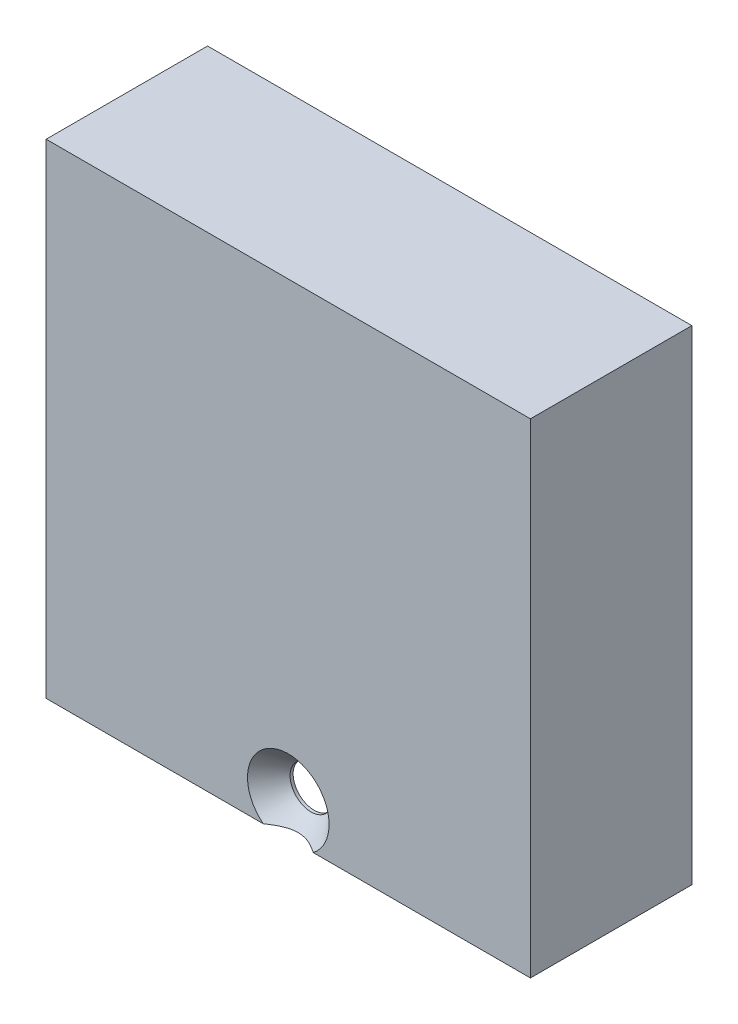
SolidWorks part; units mm, degrees
ref_plane "Plan de face" through (0, 0, 0) normal (0, 0, 1) x (1, 0, 0)
ref_plane "Plan de dessus" through (0, 0, 0) normal (0, 1, 0) x (1, 0, 0)
ref_plane "Plan de droite" through (0, 0, 0) normal (1, 0, 0) x (0, 0, -1)
sketch "Esquisse1" plane through (0, 0, 0) normal (0, 0, 1) x (1, 0, 0)
  line L1 (0, 0) -> (30, 0)
  line L2 (0, 0) -> (0, 30)
  line L3 (0, 30) -> (30, 30)
  line L4 (30, 0) -> (30, 30)
  dimension "D1" = 30
  dimension "D2" = 30
extrude "Main" add sketch "Esquisse1" along normal blind 10
sketch "Esquisse2" plane through (0, 0, 0) normal (0, -1, 0) x (1, 0, 0)
  line L0 (2.75, 0) -> (2.75, 5.2)
  line L1 (0, 0) -> (30, 0) construction
  line L2 (2.75, 5.2) -> (3.35, 5.2)
  line L3 (3.35, 5.2) -> (3.35, 6.2)
  line L4 (3.35, 6.2) -> (2.75, 6.2)
  line L5 (2.75, 6.2) -> (2.75, 8.4)
  line L6 (2.75, 8.4) -> (27.25, 8.4)
  line L7 (27.25, 8.4) -> (27.25, 6.2)
  line L8 (27.25, 6.2) -> (26.65, 6.2)
  line L9 (26.65, 6.2) -> (26.65, 5.2)
  line L10 (26.65, 5.2) -> (27.25, 5.2)
  line L11 (27.25, 5.2) -> (27.25, 0)
  line L12 (27.25, 0) -> (2.75, 0)
  line L13 (0, 10) -> (30, 10) construction
  point P13 (15, 0)
  dimension "D1" = 24.5
  dimension "D2" = 0.6
  dimension "D3" = 1
  dimension "D4" = 2.2
  dimension "D5" = 8.4
  dimension "D6" = 5.2
extrude "Main Fix" cut sketch "Esquisse2" against normal blind 28.5
sketch "Esquisse4" plane through (0, 0, 8.4) normal (0, 0, -1) x (-1, 0, 0)
  line L3 (-27.25, 28.5) -> (-27.25, 0) construction
  line L4 (-2.75, 28.5) -> (-2.75, 0) construction
  line L5 (-27.25, 15.5) -> (-27.25, 28.5)
  line L6 (-27.25, 28.5) -> (-2.75, 28.5)
  line L7 (-2.75, 28.5) -> (-2.75, 15.5)
  line L8 (-2.75, 28.5) -> (-27.25, 28.5) construction
  arc A0 (-27.25, 15.5) -> (-2.75, 15.5) centre (-15, 15.5) cw
  dimension "D1" = 12.25
  dimension "D2" = 13
extrude "Boss.-Extru.2" add sketch "Esquisse4" along normal up to surface (8.4 mm away) up to face at (15, 14.625, 0)
sketch "Esquisse5" plane through (0, 0, 5.2) normal (0, 0, -1) x (-1, 0, 0)
  line L0 (-3.35, 13.9703) -> (0, 13.9703)
  line L1 (0, 13.9703) -> (0, 30)
  line L2 (0, 30) -> (-30, 30)
  line L3 (-30, 30) -> (-30, 13.9703)
  line L4 (-30, 13.9703) -> (-26.65, 13.9703)
  line L5 (-30, 0) -> (-30, 30) construction
  line L6 (0, 30) -> (0, 0) construction
  line L7 (-30, 30) -> (0, 30) construction
  line L8 (-26.65, 19.2868) -> (-26.65, 0) construction
  arc A0 (-26.65, 13.9703) -> (-3.35, 13.9703) centre (-15, 15.5) cw
  arc A3 (-2.75, 15.5) -> (-27.25, 15.5) centre (-15, 15.5) ccw construction
  dimension "D1" = 11.75
extrude "Boss.-Extru.3" add sketch "Esquisse5" against normal up to surface (1 mm away) up to face at (26.9873, 8.7026, 6.2)
sketch "Esquisse10" plane through (0, 0, 10) normal (0, 0, 1) x (1, 0, 0)
  line L0 (0, 0) -> (30, 0) construction
  point P0 (15, 2)
  point P4 (15, 0)
  dimension "D1" = 2
hole_wizard "Fraisage pour vis à tête fraisée bombée #33" positions "Esquisse11" profile "Esquisse12" countersink size "#3" standard "Ansi Inch" end condition through all
sketch "Esquisse11" plane through (0, 0, 10) normal (0, 0, 1) x (1, 0, 0)
  point P0 (15, 2)
sketch "Esquisse12" plane through (15, 2, 10) normal (1, 0, 0) x (0, -1, 0)
  line L0 (0, 0) -> (0, 10)
  line L1 (0, 10) -> (1.3, 10)
  line L2 (1.3, 10) -> (1.3, 1.4119)
  line L3 (1.3, 1.4119) -> (2.5273, 0)
  line L5 (2.5273, 0) -> (0, 0)
  line L6 (-1.3, 1.4119) -> (-2.5273, 0) construction
  line L11 (0, -6.35) -> (0, 107.95) construction
  dimension "Diamètre du perçage jusqu'au prochain" = 2.6
  dimension "Profondeur du perçage jusqu'au prochain" = 10
  dimension "Diamètre du fraisage entrant" = 5.0546
  dimension "Angle du fraisage entrant" = 82
